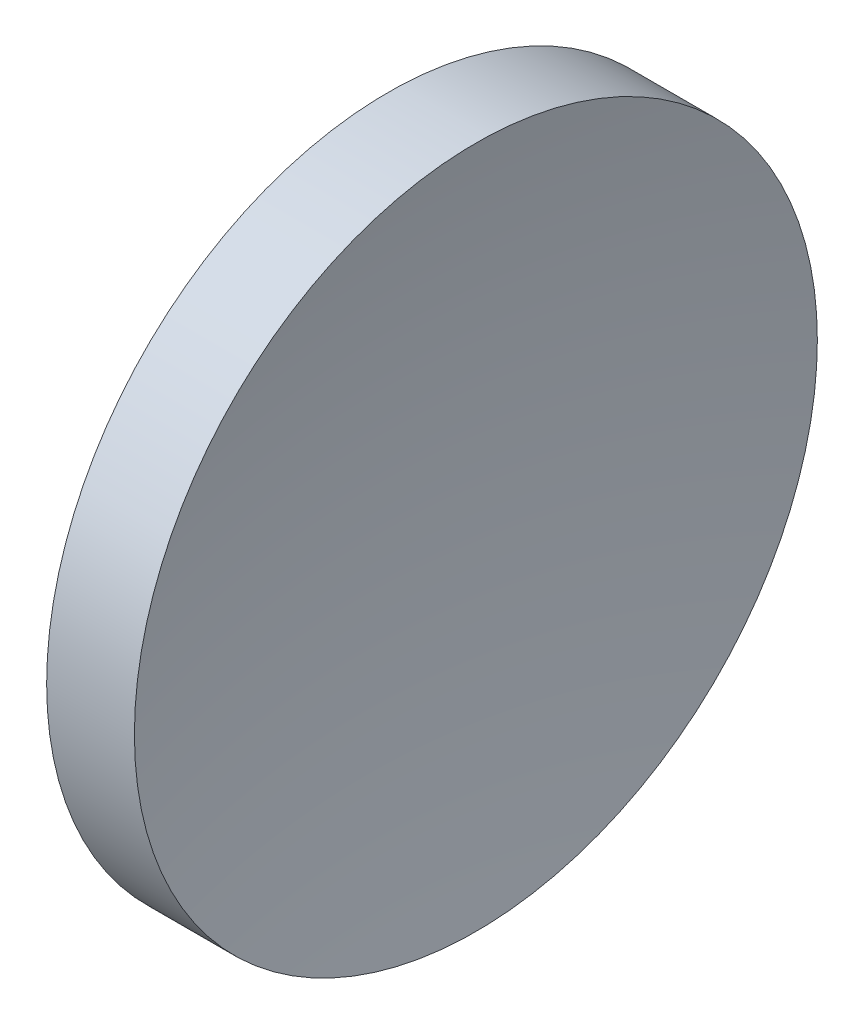
SolidWorks part; units mm, degrees
ref_plane "前视基准面" through (0, 0, 0) normal (0, 0, 1) x (1, 0, 0)
ref_plane "上视基准面" through (0, 0, 0) normal (0, 1, 0) x (1, 0, 0)
ref_plane "右视基准面" through (0, 0, 0) normal (1, 0, 0) x (0, 0, -1)
sketch "草图1" plane through (0, 0, 0) normal (0, 0, 1) x (1, 0, 0)
  line L0 (56.1009, 32.6108) -> (68.2773, 32.6108) construction
  line L1 (57.5323, 32.6108) -> (57.5323, 45.1108)
  line L2 (57.5323, 45.1108) -> (60.7449, 45.1108)
  line L3 (59.5323, 32.6108) -> (57.5323, 32.6108)
  arc A0 (60.7449, 45.1108) -> (59.5323, 32.6108) centre (124.0823, 32.6578) ccw
revolve "旋转1" add sketch "草图1" angle 360 about L0
